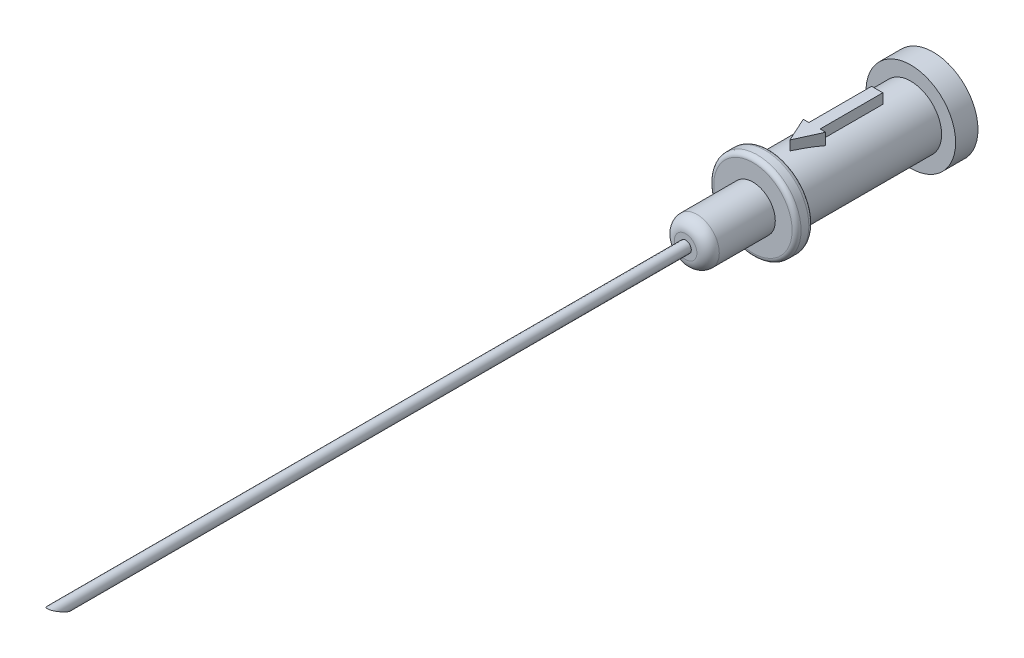
SolidWorks part; units mm, degrees
ref_plane "Front Plane" through (0, 0, 0) normal (0, 0, 1) x (1, 0, 0)
ref_plane "Top Plane" through (0, 0, 0) normal (0, 1, 0) x (1, 0, 0)
ref_plane "Right Plane" through (0, 0, 0) normal (1, 0, 0) x (0, 0, -1)
sketch "Sketch1" plane through (0, 0, 0) normal (0, 0, 1) x (1, 0, 0)
  circle A0 centre (0, 0) radius 4
  dimension "D1" = 8
extrude "Boss-Extrude1" add sketch "Sketch1" along normal blind 2
sketch "Sketch2" plane through (0, 0, 2) normal (0, 0, 1) x (1, 0, 0)
  circle A0 centre (0, 0) radius 2.75
  dimension "D1" = 5.5
extrude "Boss-Extrude2" add sketch "Sketch2" along normal blind 12.6
sketch "Sketch3" plane through (0, 0, 14.6) normal (0, 0, 1) x (1, 0, 0)
  circle A0 centre (0, 0) radius 3.9
  dimension "D1" = 7.8
extrude "Boss-Extrude3" add sketch "Sketch3" along normal blind 1.5
sketch "Sketch4" plane through (0, 0, 16.1) normal (0, 0, 1) x (1, 0, 0)
  circle A0 centre (0, 0) radius 2
  dimension "D1" = 4
extrude "Boss-Extrude4" add sketch "Sketch4" along normal blind 6
fillet "Fillet1" radius 1 1 edges at (2, 0, 22.1)
sketch "Sketch5" plane through (0, 0, 0) normal (0, 1, 0) x (1, 0, 0)
  line L0 (0, 0) -> (0, -22.639) construction
  line L1 (-2.75, -2) -> (2.75, -2) construction
  line L2 (-0.5, -5) -> (0.5, -5)
  line L3 (-0.5, -5) -> (-0.5, -10.6)
  line L4 (0.5, -10.6) -> (1, -10.6)
  line L5 (0.5, -5) -> (0.5, -10.6)
  line L6 (-1, -10.6) -> (-0.5, -10.6)
  line L7 (1, -10.6) -> (0, -12.8)
  line L8 (0, -12.8) -> (-1, -10.6)
  point P9 (0, -5)
  dimension "D1" = 3
  dimension "D2" = 5.6
  dimension "D3" = 1
  dimension "D4" = 2.2
  dimension "D5" = 1
  dimension "D6" = 1
extrude "Boss-Extrude5" add sketch "Sketch5" along normal blind 3.6
sketch "Sketch6" plane through (0, 0, 22.1) normal (0, 0, 1) x (1, 0, 0)
  circle A0 centre (0, 0) radius 0.5
  dimension "D1" = 1
extrude "Boss-Extrude6" add sketch "Sketch6" along normal blind 57
sketch "Sketch7" plane through (0, 0, 0) normal (1, 0, 0) x (0, 0, -1)
  line L0 (-79.1, 0.5) -> (-77.1, -0.5)
  line L1 (-79.1, -0.5) -> (-22.1, -0.5) construction
  line L2 (-77.1, -0.5) -> (-79.1, -0.5)
  line L3 (-79.1, 0.5) -> (-79.1, -0.5) construction
  line L4 (-79.1, -0.5) -> (-79.1, 0.5)
  dimension "D1" = 2
extrude "Cut-Extrude1" cut sketch "Sketch7" against normal through all both and the other way through all
fillet "Fillet2" radius 0.4 2 edges at (3.9, 0, 16.1) (3.9, 0, 14.6)
